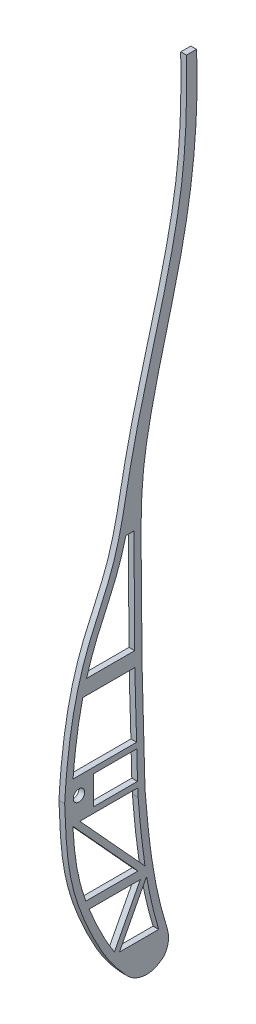
SolidWorks part; units mm, degrees
ref_plane "Front Plane" through (0, 0, 0) normal (0, 0, 1) x (1, 0, 0)
ref_plane "Top Plane" through (0, 0, 0) normal (0, 1, 0) x (1, 0, 0)
ref_plane "Right Plane" through (0, 0, 0) normal (1, 0, 0) x (0, 0, -1)
sketch "rib1" plane through (0, 0, 0) normal (1, 0, 0) x (0, 0, -1)
  line L0 (-71.2313, 530.3957) -> (928.7687, 530.3957) construction
  line L1 (884.1904, 599.9039) -> (887.9745, 599.9039)
  line L2 (856.9345, 370.6416) -> (865.0745, 370.6416)
  line L3 (850.4345, 376.6416) -> (850.4345, 379.6416)
  line L4 (850.4345, 376.6416) -> (850.4345, 373.6416)
  line L5 (840.8063, 376.6416) -> (845.8063, 376.6416) construction
  line L8 (855.8579, 382.6416) -> (843.7452, 382.6416)
  line L9 (855.8579, 382.6416) -> (864.8136, 382.6416)
  line L10 (856.9345, 368.6416) -> (844.7619, 368.6416)
  line L11 (856.9345, 368.6416) -> (865.1127, 368.6416)
  line L12 (866.2204, 340.1291) -> (848.917, 340.1291)
  line L13 (858.3122, 320.8088) -> (858.0269, 320.2668)
  line L14 (848.4203, 343.1291) -> (847.9481, 343.1291)
  line L15 (860.5104, 442.9155) -> (866.5886, 442.9155)
  line L16 (858.0269, 320.2668) -> (873.8862, 320.2668)
  line L17 (855.8579, 318.9992) -> (874.2194, 327.9134) construction
  line L18 (854.766, 321.2482) -> (871.1797, 329.2167) construction
  line L19 (871.1797, 329.2167) -> (873.8862, 320.2668)
  line L20 (843.5049, 367.0528) -> (865.4106, 343.1291)
  line L21 (866.2204, 340.1291) -> (856.8415, 322.3087)
  line L22 (844.7619, 368.6416) -> (867.7752, 343.5082)
  line L23 (868.4574, 340.0851) -> (858.3122, 320.8088)
  line L24 (865.4106, 343.1291) -> (848.4203, 343.1291)
  line L26 (856.9345, 370.6416) -> (850.4345, 370.6416)
  line L27 (850.4345, 370.6416) -> (850.4345, 373.6416)
  line L29 (855.8579, 380.6416) -> (864.9113, 380.6416)
  line L30 (855.8579, 380.6416) -> (850.4345, 380.6416)
  line L31 (850.4345, 380.6416) -> (850.4345, 379.6416)
  circle A0 centre (845.8063, 376.6416) radius 2
  arc A1 (841.0443, 380.5713) -> (847.6718, 415.72) centre (1017.3451, 365.528) cw
  arc A2 (851.2954, 425.5507) -> (861.6081, 456.6454) centre (699.0135, 493.3134) ccw
  arc A3 (862.9829, 461.9026) -> (884.1904, 599.9039) centre (374.0528, 607.6697) ccw
  arc A4 (840.7788, 371.8072) -> (855.8579, 318.9992) centre (950.1899, 374.4922) ccw
  arc A5 (867.6216, 376.9662) -> (872.8022, 332.64) centre (1022.9399, 372.6533) ccw
  arc A6 (867.6216, 376.9662) -> (871.4996, 461.3529) centre (1263.0251, 401.0778) cw
  arc A7 (871.9368, 463.9152) -> (887.9745, 599.9039) centre (-120.6116, 649.9108) ccw
  arc A8 (874.2194, 327.9134) -> (872.8022, 332.64) centre (950.104, 353.2418) cw
  arc A9 (841.0443, 380.5713) -> (840.7788, 371.8072) centre (920.7547, 373.7698) ccw
  arc A10 (851.2954, 425.5507) -> (847.6718, 415.72) centre (924.3857, 393.0268) ccw
  arc A11 (862.9829, 461.9026) -> (861.6081, 456.6454) centre (939.6482, 439.046) ccw
  arc A12 (871.4996, 461.3529) -> (871.9368, 463.9152) centre (950.5681, 449.1804) cw
  arc A13 (843.7452, 382.6416) -> (850.0691, 415.0108) centre (1017.3451, 365.528) cw
  arc A14 (853.5794, 424.5344) -> (850.0691, 415.0108) centre (924.3857, 393.0268) ccw
  arc A15 (853.5794, 424.5344) -> (860.5104, 442.9155) centre (699.0135, 493.3134) ccw
  arc A16 (843.5353, 380.3587) -> (850.0691, 415.0108) centre (1017.3451, 365.528) cw construction
  arc A17 (843.5049, 367.0528) -> (847.9481, 343.1291) centre (950.1899, 374.4922) ccw
  arc A18 (865.0721, 374.4641) -> (865.0745, 370.6416) centre (1022.9399, 372.6533) ccw
  arc A19 (864.962, 379.6766) -> (864.9113, 380.6416) centre (1263.0251, 401.0778) cw
  arc A20 (871.1797, 329.2167) -> (870.3865, 331.9962) centre (950.104, 353.2418) cw
  arc A21 (868.4574, 340.0851) -> (870.3865, 331.9962) centre (1022.9399, 372.6533) ccw
  arc A22 (865.3787, 461.1883) -> (886.6901, 599.8658) centre (374.0528, 607.6697) ccw construction
  arc A23 (865.1195, 376.9245) -> (870.3865, 331.9962) centre (1022.9399, 372.6533) ccw construction
  arc A24 (869.4795, 464.3757) -> (885.4776, 600.0277) centre (-120.6116, 649.9108) ccw construction
  arc A25 (843.278, 371.8685) -> (858.0127, 320.2668) centre (950.1899, 374.4922) ccw construction
  arc A26 (853.5794, 424.5344) -> (864.0469, 456.0955) centre (699.0135, 493.3134) ccw construction
  arc A27 (865.3787, 461.1883) -> (864.0469, 456.0955) centre (939.6482, 439.046) ccw construction
  arc A28 (865.1195, 376.9245) -> (869.0287, 461.7333) centre (1263.0251, 401.0778) cw construction
  arc A29 (869.0287, 461.7333) -> (869.4795, 464.3757) centre (950.5681, 449.1804) cw construction
  arc A30 (848.917, 340.1291) -> (856.8415, 322.3087) centre (950.1899, 374.4922) ccw
  arc A31 (865.1127, 368.6416) -> (867.7752, 343.5082) centre (1022.9399, 372.6533) ccw
  arc A32 (864.8136, 382.6416) -> (866.5886, 442.9155) centre (1263.0251, 401.0778) cw
  arc A33 (865.0721, 374.4641) -> (864.962, 379.6766) centre (785.0773, 375.3817) ccw
  spline S0 degree 3 poles (855.8579, 318.9992) (859.3648, 313.0596) (867.0534, 309.8477) (875.8907, 311.5767) (877.0472, 317.8757) (875.7309, 323.2627) (874.9921, 325.5984) (874.2194, 327.9134) knots 0 0 0 0 0.275026 0.518183 0.708506 0.751927 0.952395 0.952395 0.952395 0.952395
  dimension "D2" = 2.5
  dimension "D1" = 1000
sketch "rib2" plane through (0, 0, 0) normal (1, 0, 0) x (0, 0, -1)
  line L0 (-154.4211, 376.6416) -> (49845.5789, 376.6416) construction
  line L1 (-144.1421, 380.6416) -> (49855.8579, 380.6416) construction
  line L2 (-143.0655, 370.6416) -> (49856.9345, 370.6416) construction
  line L3 (782.8933, 343.3859) -> (760.3563, 368.2109)
  line L4 (-143.0655, 368.6416) -> (49856.9345, 368.6416) construction
  line L5 (-144.1421, 382.6416) -> (49855.8579, 382.6416) construction
  line L6 (785.2354, 343.762) -> (762.6647, 368.6416)
  line L7 (764.6298, 343.3859) -> (782.8933, 343.3859)
  line L8 (783.7374, 340.3859) -> (774.2204, 321.3554)
  line L9 (767.5719, 380.6416) -> (767.5719, 370.6416)
  line L10 (767.5719, 370.6416) -> (782.7291, 370.6416)
  line L11 (767.5719, 380.6416) -> (782.2855, 380.6416)
  line L12 (765.5126, 340.3859) -> (783.7374, 340.3859)
  line L13 (762.6647, 368.6416) -> (782.7755, 368.6416)
  line L14 (776.5435, 321.5294) -> (789.8459, 321.5294)
  line L15 (760.7138, 382.6416) -> (782.1585, 382.6416)
  line L16 (770.7866, 427.4918) -> (781.8144, 427.4918)
  line L17 (801.9062, 590.4081) -> (805.115, 590.4081)
  line L18 (757.9166, 376.6416) -> (762.9166, 376.6416) construction
  line L20 (785.9296, 340.298) -> (776.5435, 321.5294)
  circle A0 centre (762.9166, 376.6416) radius 2
  arc A1 (758.9972, 388.4269) -> (758.7602, 360.0657) centre (857.8646, 373.419) ccw
  spline S0 degree 3 poles (758.7602, 360.0657) (759.4545, 354.9126) (761.6392, 342.918) (767.6025, 326.3565) (776.3644, 313.1833) (785.8807, 308.842) (791.3139, 310.6103) (793.0754, 312.9879) (793.3375, 316.1077) (791.0414, 329.6431) (787.956, 341.1966) (785.2042, 359.6207) (785.4538, 372.9971) (783.4315, 397.4301) (785.2476, 420.7625) (783.0535, 455.8097) (784.4694, 464.3867) (788.1328, 479.2935) (793.2428, 503.9805) (802.5401, 542.6054) (805.2587, 572.3941) (805.115, 590.4081) knots 0.028705 0.028705 0.028705 0.028705 0.059247 0.100348 0.1322 0.149146 0.158796 0.160734 0.16766 0.175847 0.234409 0.24607 0.285136 0.310616 0.385264 0.441942 0.454033 0.506165 0.624061 0.777474 1 1 1 1
  spline S1 degree 3 poles (801.9062, 590.4081) (801.6966, 560.1521) (794.9988, 516.4373) (781.9369, 464.9221) (769.955, 434.3358) (762.9603, 410.299) (759.9193, 394.5015) (758.9972, 388.4269) knots 0 0 0 0 0.408823 0.598513 0.719262 0.854061 0.937351 0.937351 0.937351 0.937351
  spline S2 degree 3 poles (760.3563, 368.2109) (760.6455, 365.1083) (761.2971, 359.3998) (762.6856, 351.2079) (763.8909, 346.0643) (764.604, 343.4789) (764.6298, 343.3859) knots 0.01313 0.01313 0.01313 0.01313 0.031626 0.047245 0.062864 0.063447 0.063447 0.063447 0.063447
  spline S3 degree 3 poles (765.5126, 340.3859) (765.9421, 339.0082) (767.2255, 335.1967) (769.2617, 330.2911) (771.6089, 325.6402) (773.0967, 323.06) (774.0043, 321.6748) (774.2204, 321.3554) knots 0.069751 0.069751 0.069751 0.069751 0.078483 0.094102 0.101912 0.109721 0.112105 0.112105 0.112105 0.112105
  spline S5 degree 3 poles (782.7291, 370.6416) (782.7064, 371.5634) (782.6438, 373.8426) (782.4996, 377.1608) (782.3523, 379.5799) (782.2855, 380.6416) knots 0.276245 0.276245 0.276245 0.276245 0.281529 0.289339 0.295445 0.295445 0.295445 0.295445
  spline S6 degree 3 poles (789.8459, 321.5294) (789.8142, 321.6995) (789.7504, 322.0389) (789.4577, 323.5807) (788.9295, 326.2404) (788.1496, 329.9526) (787.3325, 333.724) (786.5882, 337.1579) (786.1256, 339.3494) (785.9296, 340.298) knots 0.178918 0.178918 0.178918 0.178918 0.179894 0.18087 0.187816 0.195625 0.203435 0.211244 0.21717 0.21717 0.21717 0.21717
  spline S7 degree 3 poles (785.2354, 343.762) (784.9117, 345.4358) (784.3695, 348.4126) (783.6834, 352.846) (783.0923, 358.3507) (782.8866, 363.6197) (782.8011, 367.501) (782.7755, 368.6416) knots 0.224345 0.224345 0.224345 0.224345 0.234672 0.242482 0.250291 0.26591 0.27243 0.27243 0.27243 0.27243
  spline S8 degree 3 poles (782.1585, 382.6416) (782.0098, 384.985) (781.5323, 392.7288) (781.6016, 402.5045) (781.8121, 413.0284) (781.8895, 420.0466) (781.8563, 425.0079) (781.8229, 427.0307) (781.8144, 427.4918) knots 0.299279 0.299279 0.299279 0.299279 0.312767 0.344005 0.359624 0.375243 0.383052 0.385336 0.385336 0.385336 0.385336
  spline S9 degree 3 poles (770.7866, 427.4918) (769.4671, 423.3387) (766.9647, 414.7701) (763.3804, 399.8515) (761.5251, 389.0141) (760.7138, 382.6416) knots 0.752168 0.752168 0.752168 0.752168 0.811773 0.874217 0.962264 0.962264 0.962264 0.962264
  point P26 (765.5126, 340.3859)
  point P30 (764.6298, 343.3859)
  point P35 (774.2204, 321.3554)
  point P36 (789.8459, 321.5294)
  point P37 (785.9296, 340.298)
  point P39 (760.3563, 368.2109)
  point P40 (760.0729, 371.4986)
  dimension "D1" = 100
sketch "Sketch5" plane through (0, 0, 0) normal (1, 0, 0) x (0, 0, -1)
  line L0 (-200154.4211, 376.6416) -> (249845.5789, 376.6416) construction
  line L1 (693.317, 322.1015) -> (707.0464, 322.1015)
  line L2 (695.5696, 447.1101) -> (698.3736, 447.1101)
  line L3 (698.6642, 410.7316) -> (681.8197, 410.7316)
  line L4 (698.7261, 405.5878) -> (680.4847, 405.5878)
  line L5 (677.0801, 382.6416) -> (699.3215, 382.6416)
  line L7 (699.7026, 368.6416) -> (679.4803, 368.6416)
  line L8 (-200143.0655, 368.6416) -> (249856.9345, 368.6416) construction
  line L9 (674.1545, 376.6416) -> (679.1545, 376.6416) construction
  line L10 (684.2181, 380.6416) -> (684.2181, 370.6416)
  line L11 (-200144.1421, 380.6416) -> (249855.8579, 380.6416) construction
  line L12 (-200143.0655, 370.6416) -> (249856.9345, 370.6416) construction
  line L13 (684.2181, 370.6416) -> (699.6248, 370.6416)
  line L14 (702.2048, 368.6416) -> (702.335, 365.9116)
  line L15 (699.3639, 380.6416) -> (684.2181, 380.6416)
  line L16 (708.485, 312.754) -> (708.6651, 312.9152)
  line L17 (706.7921, 314.6987) -> (706.9599, 314.7434)
  line L18 (699.8434, 365.7077) -> (699.7071, 368.5354)
  line L19 (682.1263, 343.4207) -> (681.5591, 343.4207)
  line L20 (700.6109, 340.4181) -> (682.6985, 340.4181)
  line L21 (699.3639, 380.6416) -> (699.6248, 370.6416)
  line L22 (705.0572, 343.4207) -> (704.8181, 343.4207)
  line L23 (716.7384, 582.0418) -> (720.2752, 582.0418)
  line L24 (693.317, 322.1015) -> (702.7962, 340.2834)
  line L25 (702.2445, 343.7103) -> (679.4803, 368.6416)
  line L26 (691.5466, 323.0319) -> (700.6109, 340.4181)
  line L28 (699.8006, 343.4207) -> (682.1263, 343.4207)
  line L32 (699.8006, 343.4207) -> (677.0187, 368.3713)
  circle A0 centre (679.1545, 376.6416) radius 2
  spline S0 degree 3 poles (674.1545, 376.6416) (674.6209, 363.9047) (675.4244, 348.9718) (687.0005, 324.6734) (691.715, 318.3055) (697.5054, 311.9056) (699.9912, 310.5046) (704.8962, 310.5781) (707.1739, 311.6254) (708.485, 312.754) knots 0 0 0 0 0.082297 0.137777 0.177735 0.177735 0.194632 0.194632 0.2043 0.2043 0.2043 0.2043
  spline S1 degree 3 poles (716.7384, 582.0418) (716.9491, 569.6586) (716.384, 531.2528) (699.2016, 484.7456) (692.8166, 441.1757) (677.838, 413.403) (675.0171, 391.1698) (674.1545, 376.6416) knots 0 0 0 0 0.169562 0.555938 0.689283 0.791056 1 1 1 1
  spline S2 degree 3 poles (702.2445, 343.7103) (702.1641, 344.2407) (701.7657, 346.9448) (701.1382, 351.8745) (700.5581, 357.5193) (700.1402, 362.1447) (699.9401, 364.5255) (699.8434, 365.7077) knots 0.317112 0.317112 0.317112 0.317112 0.32289 0.346516 0.370142 0.381955 0.393768 0.393768 0.393768 0.393768
  spline S4 degree 3 poles (702.2048, 368.6416) (701.8669, 376.5926) (701.8555, 384.7425) (701.1266, 402.784) (701.1396, 431.7405) (700.5544, 456.9254) (705.1133, 487.005) (717.5576, 525.1697) (721.078, 562.1394) (720.2752, 582.0418) knots 0.402967 0.402967 0.402967 0.402967 0.483086 0.483086 0.591391 0.687653 0.687653 0.844633 1 1 1 1
  spline S5 degree 3 poles (699.3215, 382.6416) (699.3024, 383.5334) (699.2425, 386.2646) (699.1476, 389.8671) (699.0014, 393.4021) (698.878, 397.2735) (698.7899, 401.3622) (698.7401, 404.5905) (698.7261, 405.5878) knots 0.449941 0.449941 0.449941 0.449941 0.458939 0.477596 0.486925 0.496254 0.514911 0.523067 0.523067 0.523067 0.523067
  spline S6 degree 3 poles (699.7071, 368.5354) (699.7056, 368.5708) (699.7041, 368.6062) (699.7026, 368.6416) knots 0.402967 0.402967 0.402967 0.402967 0.40332 0.40332 0.40332 0.40332
  spline S7 degree 3 poles (682.6985, 340.4181) (683.0121, 339.6321) (683.9949, 337.2558) (685.7648, 333.3639) (687.9735, 329.011) (689.7493, 325.8616) (690.8989, 324.0094) (691.3927, 323.2607) (691.5466, 323.0319) knots 0.095831 0.095831 0.095831 0.095831 0.10215 0.114919 0.127687 0.140456 0.14684 0.149678 0.149678 0.149678 0.149678
  spline S8 degree 3 poles (677.0187, 368.3713) (677.0192, 368.3626) (677.0681, 367.4934) (677.2257, 364.9551) (677.5669, 360.9606) (678.1637, 356.4034) (679.0103, 351.9539) (680.1158, 347.6804) (681.0683, 344.7879) (681.5591, 343.4207) knots 0.019088 0.019088 0.019088 0.019088 0.019153 0.025537 0.038306 0.051075 0.063844 0.076612 0.087747 0.087747 0.087747 0.087747
  spline S9 degree 3 poles (708.6651, 312.9152) (709.0596, 313.2832) (711.3268, 316.9807) (705.4793, 334.2076) (703.6294, 350.0939) (702.335, 365.9116) knots 0.204759 0.204759 0.204759 0.204759 0.207895 0.236848 0.393768 0.393768 0.393768 0.393768
  spline S10 degree 3 poles (676.659, 376.6416) (676.6584, 376.6321) (676.6578, 376.6225) (676.6573, 376.613) knots 0.999862 0.999862 0.999862 0.999862 1 1 1 1
  spline S11 degree 3 poles (707.0464, 322.1015) (707.0052, 322.2371) (706.9227, 322.5094) (706.5342, 323.8003) (705.9077, 326.017) (705.0863, 329.1749) (704.0811, 333.4582) (703.3421, 337.155) (702.8797, 339.7948) (702.7962, 340.2834) knots 0.237993 0.237993 0.237993 0.237993 0.239469 0.240946 0.252011 0.263824 0.275637 0.299263 0.304623 0.304623 0.304623 0.304623
  spline S12 degree 3 poles (680.4847, 405.5878) (680.2388, 404.5378) (679.0822, 399.2686) (677.9122, 391.5905) (677.2696, 384.9533) (677.0801, 382.6416) knots 0.859357 0.859357 0.859357 0.859357 0.875 0.9375 0.970921 0.970921 0.970921 0.970921
  spline S13 degree 3 poles (698.6642, 410.7316) (698.6438, 412.7052) (698.5832, 419.5769) (698.503, 431.741) (698.3426, 441.7088) (698.3711, 446.7739) (698.3736, 447.1101) knots 0.536769 0.536769 0.536769 0.536769 0.552225 0.58954 0.626855 0.629511 0.629511 0.629511 0.629511
  spline S15 degree 3 poles (695.5696, 447.1101) (695.4451, 446.6155) (694.7557, 443.952) (693.3092, 439.1408) (690.7575, 432.8707) (687.9819, 426.8359) (685.294, 420.8884) (683.2818, 415.5566) (682.219, 412.126) (681.8197, 410.7316) knots 0.649129 0.649129 0.649129 0.649129 0.65625 0.6875 0.71875 0.75 0.78125 0.8125 0.833615 0.833615 0.833615 0.833615
sketch "Sketch6" plane through (0, 0, 0) normal (1, 0, 0) x (0, 0, -1)
  line L0 (-200154.4211, 376.6416) -> (249845.5789, 376.6416) construction
  line L1 (594.2077, 382.6416) -> (615.9917, 382.6416)
  line L2 (-200144.1421, 382.6416) -> (249855.8579, 382.6416) construction
  line L3 (617.0002, 368.6416) -> (597.1315, 368.6416)
  line L4 (-200143.0655, 368.6416) -> (249856.9345, 368.6416) construction
  line L7 (609.0006, 321.5886) -> (608.931, 321.4458)
  line L8 (610.7981, 320.7115) -> (610.2002, 319.4863)
  line L9 (594.4326, 368.6416) -> (594.0581, 368.6416)
  line L11 (594.4326, 368.6416) -> (617.3118, 343.3906)
  line L12 (618.1756, 340.3906) -> (609.0006, 321.5886)
  line L13 (597.1315, 368.6416) -> (619.7239, 343.7071)
  line L23 (620.3211, 340.2268) -> (610.7981, 320.7115)
  line L28 (618.1756, 340.3906) -> (599.7563, 340.3906)
  line L29 (617.3118, 343.3906) -> (598.7382, 343.3906)
  arc A0 (610.8725, 452.2517) -> (615.4146, 451.3048) centre (613.0575, 451.3657) cw
  spline S0 degree 3 poles (591.4519, 376.6416) (590.8724, 355.6832) (598.0127, 330.747) (614.7237, 309.0913) (626.4002, 308.0944) (627.1878, 324.0074) (622.1741, 339.2467) (620.5135, 359.7877) (618.195, 380.0068) (618.3402, 403.8303) (616.7499, 433.3564) (618.9592, 474.5213) (631.6465, 520.1908) (636.0177, 556.3417) (635.098, 572.5915) knots 0 0 0 0 0.181753 0.211103 0.236632 0.255743 0.327686 0.385848 0.430346 0.504499 0.591378 0.686471 0.859586 1 1 1 1
  spline S1 degree 3 poles (632.3767, 572.5915) (632.331, 559.797) (630.7518, 538.4728) (623.6454, 509.5847) (617.1086, 483.6159) (609.1878, 456.4292) (602.6277, 431.1093) (594.4581, 405.0022) (591.6906, 387.7261) (591.4519, 376.6416) knots 0 0 0 0 0.191351 0.317516 0.443871 0.591483 0.740453 0.834547 1 1 1 1
  spline S2 degree 3 poles (619.7239, 343.7071) (619.5881, 344.5842) (619.2022, 347.2732) (618.6764, 351.7986) (618.1443, 357.2765) (617.6179, 362.6875) (617.2186, 366.4692) (617.0187, 368.4566) (617.0002, 368.6416) knots 0.33611 0.33611 0.33611 0.33611 0.343735 0.359361 0.374986 0.390612 0.406237 0.40784 0.40784 0.40784 0.40784
  spline S3 degree 3 poles (599.7563, 340.3906) (599.7882, 340.3011) (600.4188, 338.5434) (601.7436, 335.154) (603.9399, 330.3213) (606.3333, 325.742) (608.0626, 322.8243) (608.931, 321.4458) knots 0.108518 0.108518 0.108518 0.108518 0.109355 0.124981 0.140606 0.156231 0.170688 0.170688 0.170688 0.170688
  spline S4 degree 3 poles (610.8725, 452.2517) (610.269, 449.893) (608.8998, 444.6758) (606.7371, 436.6294) (604.5222, 428.0779) (602.3578, 419.4861) (600.0573, 410.8763) (597.5945, 402.3898) (595.6103, 393.891) (594.6157, 387.2692) (594.2744, 383.5122) (594.2077, 382.6416) knots 0.448611 0.448611 0.448611 0.448611 0.500019 0.562521 0.625024 0.687526 0.750029 0.812531 0.875033 0.937536 0.956374 0.956374 0.956374 0.956374
  spline S5 degree 3 poles (594.0581, 368.6416) (594.1057, 367.7673) (594.4036, 363.3735) (595.4715, 355.4692) (597.3077, 347.9625) (598.5477, 343.9825) (598.7382, 343.3906) knots 0.023466 0.023466 0.023466 0.023466 0.031229 0.062479 0.09373 0.09921 0.09921 0.09921 0.09921
  spline S6 degree 3 poles (610.2002, 319.4863) (610.3292, 319.2923) (610.9476, 318.3692) (612.075, 316.7416) (613.5938, 314.8775) (615.268, 313.3623) (617.1903, 312.2288) (619.6971, 311.4612) (621.7209, 311.3604) (622.8414, 311.5923) (623.3355, 311.851) (623.4973, 312.0037) (623.7734, 312.4798) (624.0122, 313.3728) (624.1915, 314.9548) (624.1754, 317.4057) (624.0268, 320.2009) (623.7469, 322.9038) (623.3647, 325.5305) (622.9006, 328.1059) (622.2032, 331.5008) (621.2956, 335.4836) (620.6086, 338.7108) (620.3211, 340.2268) knots 0.177597 0.177597 0.177597 0.177597 0.179669 0.187482 0.195295 0.203107 0.21092 0.218733 0.226545 0.230452 0.234358 0.238264 0.242171 0.246077 0.249983 0.257796 0.265609 0.273421 0.281234 0.289047 0.296859 0.312485 0.325931 0.325931 0.325931 0.325931
  spline S7 degree 3 poles (615.9917, 382.6416) (615.8973, 385.0577) (615.7504, 391.1062) (615.6642, 400.7347) (615.3415, 411.5075) (614.9499, 422.3472) (614.7472, 433.2494) (614.9316, 442.9184) (615.2536, 448.9371) (615.4146, 451.3048) knots 0.447995 0.447995 0.447995 0.447995 0.468738 0.499989 0.53124 0.56249 0.593741 0.624992 0.645293 0.645293 0.645293 0.645293
extrude "Boss-Extrude4" add sketch "Sketch5" along normal blind 2
equation "\"1000mmm\"=767.321"
